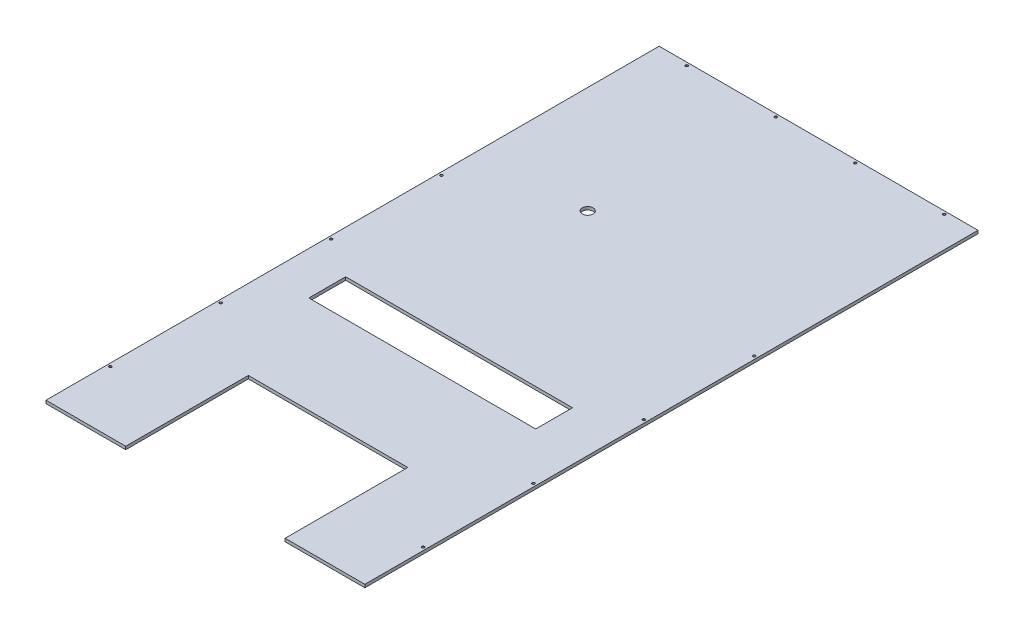
SolidWorks part; units mm, degrees
ref_plane "Front Plane" through (0, 0, 0) normal (0, 0, 1) x (1, 0, 0)
ref_plane "Top Plane" through (0, 0, 0) normal (0, 1, 0) x (1, 0, 0)
ref_plane "Right Plane" through (0, 0, 0) normal (1, 0, 0) x (0, 0, -1)
sketch "Sketch1" plane through (0, 0, 0) normal (0, 0, 1) x (1, 0, 0)
  line L1 (0, 0) -> (1320.8, 0)
  line L2 (0, 0) -> (0, 12.7)
  line L3 (0, 12.7) -> (1320.8, 12.7)
  line L4 (1320.8, 0) -> (1320.8, 12.7)
  dimension "D1" = 1320.8
  dimension "D2" = 12.7
extrude "Boss-Extrude1" add sketch "Sketch1" along normal blind 2540
sketch "Sketch2" plane through (0, 12.7, 0) normal (0, 1, 0) x (1, 0, 0)
  line L0 (330.2, -2540) -> (330.2, -2032)
  line L1 (1320.8, -2540) -> (0, -2540) construction
  line L2 (330.2, -2032) -> (990.6, -2032)
  line L3 (990.6, -2032) -> (990.6, -2540)
  line L4 (990.6, -2540) -> (330.2, -2540)
  line L7 (0, -2540) -> (0, 0) construction
  dimension "D1" = 508
  dimension "D2" = 660.4
  dimension "D3" = 330.2
extrude "Cut-Extrude1" cut sketch "Sketch2" against normal through all contours L2 L3 L4 L0
hole_wizard "3/8 (0.375) Diameter Hole1" positions "Sketch3" profile "Sketch4" hole size "3/8" standard "ANSI Inch" end condition through all
sketch "Sketch3" plane through (0, 12.7, 0) normal (0, 1, 0) x (1, 0, 0)
  line L0 (1320.8, -2540) -> (1320.8, 0) construction
  line L1 (0, -1270) -> (1500.7176, -1270) construction
  line L2 (0, -2540) -> (0, 0) construction
  line L4 (660.4, 0) -> (660.4, -2026.4593) construction
  line L5 (1320.8, 0) -> (0, 0) construction
  line L7 (1320.8, -2540) -> (990.6, -2540) construction
  point P0 (1308.1, -2286)
  point P2 (1308.1, -1828.8)
  point P4 (1308.1, -1371.6)
  point P6 (1308.1, -914.4)
  point P25 (12.7, -2286)
  point P26 (12.7, -1828.8)
  point P27 (12.7, -1371.6)
  point P28 (12.7, -914.4)
  point P29 (495.3, -12.7)
  point P31 (127, -12.7)
  point P35 (1193.8, -12.7)
  point P36 (825.5, -12.7)
  dimension "D1" = 12.7
  dimension "D2" = 254
  dimension "D3" = 457.2
  dimension "D4" = 457.2
  dimension "D5" = 457.2
  dimension "D6" = 12.7
  dimension "D7" = 127
  dimension "D8" = 165.1
sketch "Sketch4" plane through (1308.1, 12.7, 2286) normal (1, 0, 0) x (0, 0, 1)
  line L0 (0, 0) -> (0, 12.7)
  line L1 (0, 12.7) -> (4.7625, 12.7)
  line L2 (4.7625, 12.7) -> (4.7625, 0.635)
  line L3 (4.7625, 0.635) -> (5.3975, 0)
  line L5 (5.3975, 0) -> (0, 0)
  line L6 (-4.7625, 0.635) -> (-5.3975, 0) construction
  line L11 (0, -6.35) -> (0, 107.95) construction
  dimension "Thru Hole Dia." = 9.525
  dimension "Thru Hole Depth" = 12.7
  dimension "Near C'Sink Dia." = 10.795
  dimension "Near C'Sink Angle" = 90
sketch "Sketch5" plane through (0, 12.7, 0) normal (0, 1, 0) x (1, 0, 0)
  line L10 (177.8, -1628.902) -> (1117.6, -1628.902)
  line L11 (177.8, -1628.902) -> (177.8, -1476.502)
  line L12 (177.8, -1476.502) -> (1117.6, -1476.502)
  line L13 (1117.6, -1628.902) -> (1117.6, -1476.502)
  dimension "D1" = 403.098
  dimension "D2" = 152.4
  dimension "D3" = 127
  dimension "D4" = 152.4
extrude "Cut-Extrude3" cut sketch "Sketch5" against normal through all both and the other way through all
sketch "Sketch6" plane through (0, 12.7, 0) normal (0, 1, 0) x (1, 0, 0)
  circle A0 centre (442.9778, -738.9739) radius 22.225
extrude "Cut-Extrude4" cut sketch "Sketch6" against normal blind 31.75
